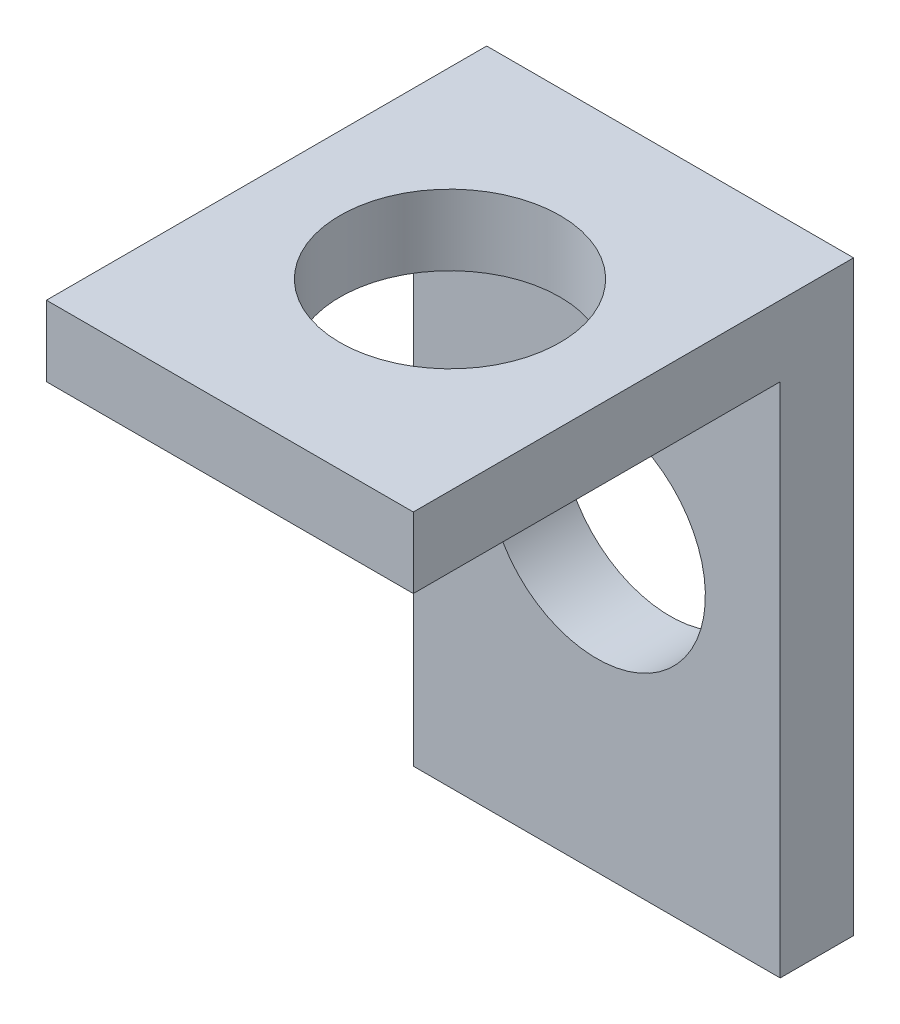
SolidWorks part; units mm, degrees
material "Chrome Stainless Steel"
ref_plane "Front Plane" through (0, 0, 0) normal (0, 0, 1) x (1, 0, 0)
ref_plane "Top Plane" through (0, 0, 0) normal (0, 1, 0) x (1, 0, 0)
ref_plane "Right Plane" through (0, 0, 0) normal (1, 0, 0) x (0, 0, -1)
sketch "Sketch1" plane through (0, 0, 0) normal (1, 0, 0) x (0, 0, -1)
  line L0 (0, 0) -> (0, -17.8745)
  line L1 (0, -17.8745) -> (2.54, -17.8745)
  line L2 (2.54, -17.8745) -> (2.54, 2.4455)
  line L5 (-12.7, 2.4455) -> (-12.7, 0)
  line L6 (-12.7, 0) -> (0, 0)
  line L7 (-12.7, 2.4455) -> (2.54, 2.4455)
  dimension "D1" = 2.4455
  dimension "D2" = 2.54
  dimension "D4" = 20.32
  dimension "D5" = 12.7
extrude "Boss-Extrude1" add sketch "Sketch1" along normal mid plane 12.7
ref_plane "Plane1" through (0, 0, -2.54) normal (0, 0, -1) x (-1, 0, 0)
sketch "Sketch6" plane through (0, 0, -2.54) normal (0, 0, -1) x (-1, 0, 0)
  line L0 (-6.35, 2.4455) -> (6.35, 2.4455) construction
  line L3 (6.35, -17.8745) -> (6.35, 2.4455) construction
  circle A0 centre (0, -7.7145) radius 3.7601
  dimension "D1" = 7.5202
  dimension "D2" = 10.16
  dimension "D3" = 6.35
extrude "Cut-Extrude3" cut sketch "Sketch6" against normal blind 12.7
ref_plane "Plane3" through (0, 2.4455, 0) normal (0, 1, 0) x (1, 0, 0)
sketch "Sketch7" plane through (0, 2.4455, 0) normal (0, 1, 0) x (1, 0, 0)
  line L0 (6.985, 2.54) -> (-6.985, 2.54) construction
  line L2 (6.35, 2.54) -> (6.35, -12.7) construction
  circle A0 centre (0, -8.89) radius 3.81
  dimension "D1" = 7.62
  dimension "D2" = 11.43
  dimension "D3" = 6.35
ref_plane "Plane4" through (0, 2.4455, 0) normal (0, 1, 0) x (1, 0, 0)
sketch "Sketch8" plane through (0, 2.4455, 0) normal (0, 1, 0) x (1, 0, 0)
  line L0 (6.985, 2.54) -> (-6.985, 2.54) construction
  line L3 (6.35, 2.54) -> (6.35, -12.7) construction
  circle A0 centre (0, -5.08) radius 3.81
  point P7 (6.35, -5.0448)
  dimension "D1" = 7.62
  dimension "D2" = 7.62
  dimension "D3" = 6.35
extrude "Cut-Extrude4" cut sketch "Sketch8" against normal blind 2.54
